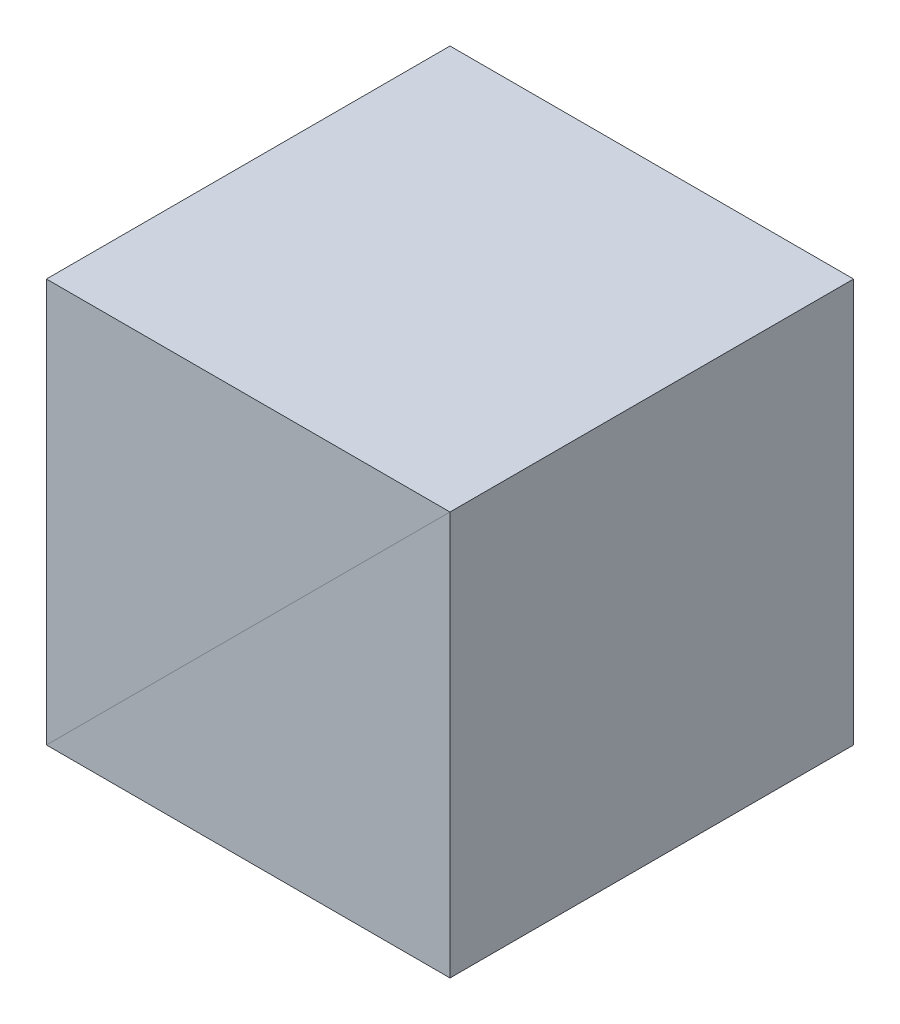
SolidWorks part; units mm, degrees
ref_plane "前视基准面" through (0, 0, 0) normal (0, 0, 1) x (1, 0, 0)
ref_plane "上视基准面" through (0, 0, 0) normal (0, 1, 0) x (1, 0, 0)
ref_plane "右视基准面" through (0, 0, 0) normal (1, 0, 0) x (0, 0, -1)
sketch "草图1" plane through (0, 0, 0) normal (0, 0, 1) x (1, 0, 0)
  line L3 (-5, -5) -> (5, -5)
  line L4 (5, 5) -> (5, -5)
  line L5 (5, 5) -> (-5, -5)
  dimension "D1" = 10
extrude "凸台-拉伸1" add sketch "草图1" along normal mid plane 10
mirror "镜向2" about plane through (5, 5, 5) normal (0.7071, -0.7071, 0) of bodies 107
